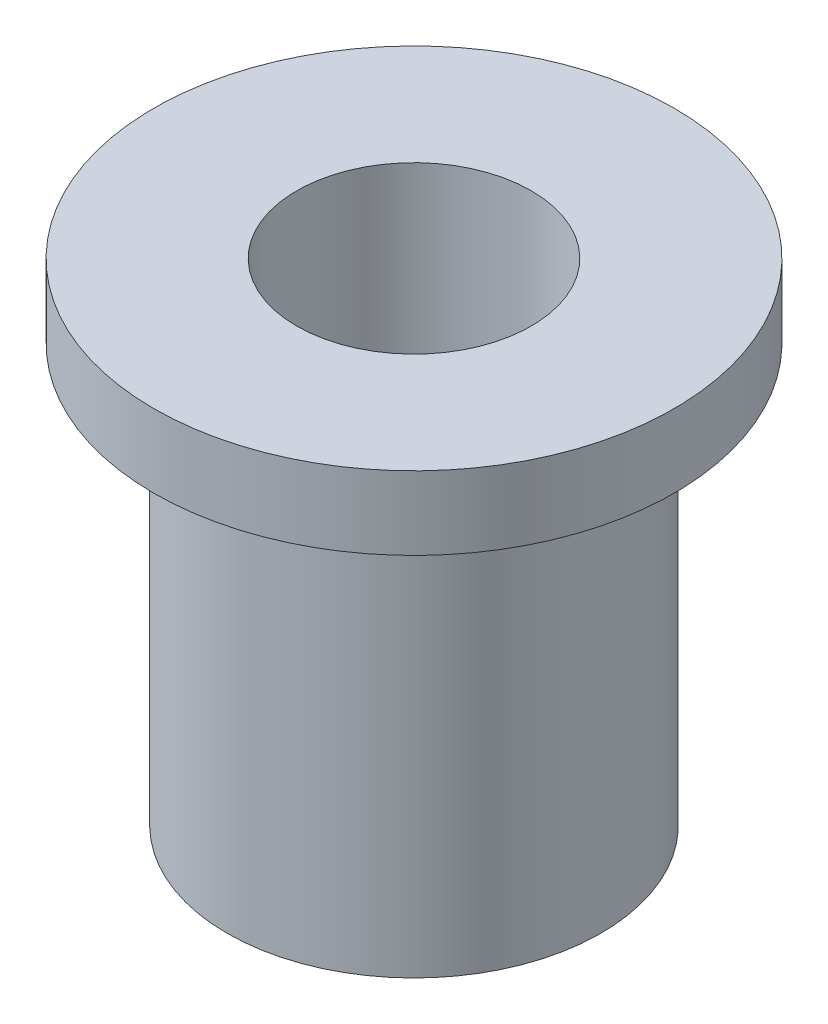
SolidWorks part; units mm, degrees
ref_plane "Front Plane" through (0, 0, 0) normal (0, 0, 1) x (1, 0, 0)
ref_plane "Top Plane" through (0, 0, 0) normal (0, 1, 0) x (1, 0, 0)
ref_plane "Right Plane" through (0, 0, 0) normal (1, 0, 0) x (0, 0, -1)
sketch "Sketch1" plane through (0, 0, 0) normal (0, 1, 0) x (1, 0, 0)
  circle A0 centre (0, 0) radius 2.55
  circle A1 centre (0, 0) radius 1.6
  dimension "D1" = 5.1
  dimension "D2" = 3.2
extrude "Boss-Extrude1" add sketch "Sketch1" along normal blind 6.7
sketch "Sketch2" plane through (0, 6.7, 0) normal (0, 1, 0) x (1, 0, 0)
  circle A0 centre (0, 0) radius 1.6
  circle A1 centre (0, 0) radius 3.55
  circle A2 centre (0, 0) radius 2.55 construction
  dimension "D1" = 1
extrude "Boss-Extrude2" add sketch "Sketch2" against normal blind 1
